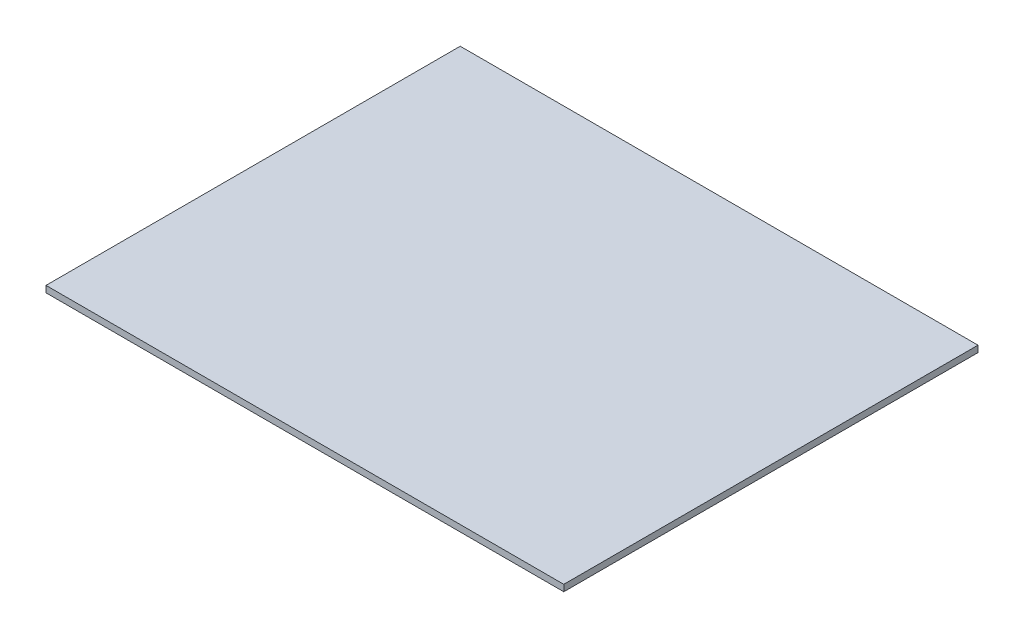
SolidWorks part; units mm, degrees
ref_plane "前视基准面" through (0, 0, 0) normal (0, 0, 1) x (1, 0, 0)
ref_plane "上视基准面" through (0, 0, 0) normal (0, 1, 0) x (1, 0, 0)
ref_plane "右视基准面" through (0, 0, 0) normal (1, 0, 0) x (0, 0, -1)
sketch "草图1" plane through (0, 0, 0) normal (0, 1, 0) x (1, 0, 0)
  line L1 (0, 0) -> (4000, 0)
  line L2 (0, 0) -> (0, 3200)
  line L3 (0, 3200) -> (4000, 3200)
  line L4 (4000, 0) -> (4000, 3200)
  dimension "D1" = 3200
  dimension "D2" = 4000
extrude "凸台-拉伸1" add sketch "草图1" along normal blind 50
